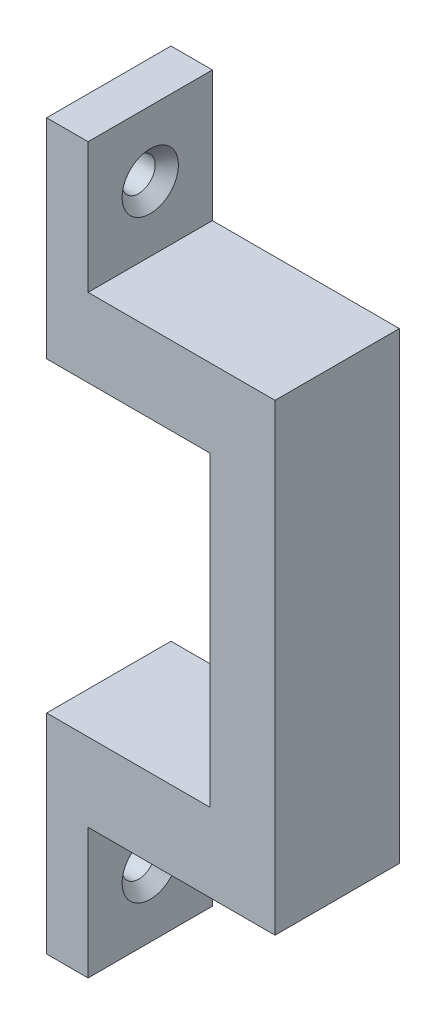
SolidWorks part; units mm, degrees
material "ABS"
ref_plane "Front" through (0, 0, 0) normal (0, 0, 1) x (1, 0, 0)
ref_plane "Top" through (0, 0, 0) normal (0, 1, 0) x (1, 0, 0)
ref_plane "Right" through (0, 0, 0) normal (1, 0, 0) x (0, 0, -1)
sketch "Sketch1" plane through (0, 0, 0) normal (0, 0, 1) x (1, 0, 0)
  line L0 (0, 11.75) -> (0, -11.75)
  line L1 (0, 11.75) -> (-12.5, 11.75)
  line L2 (-12.5, 11.75) -> (-12.5, 27.75)
  line L3 (-12.5, 27.75) -> (-9.325, 27.75)
  line L4 (-9.325, 27.75) -> (-9.325, 17.75)
  line L5 (-9.325, 17.75) -> (5, 17.75)
  line L6 (5, 17.75) -> (5, -17.75)
  line L7 (5, -17.75) -> (-9.325, -17.75)
  line L8 (-9.325, -17.75) -> (-9.325, -27.75)
  line L9 (-9.325, -27.75) -> (-12.5, -27.75)
  line L10 (-12.5, -27.75) -> (-12.5, -11.75)
  line L11 (-12.5, -11.75) -> (0, -11.75)
  point P4 (0, 0)
  dimension "D1" = 12.5
  dimension "D2" = 23.5
  dimension "D3" = 6
  dimension "D4" = 5
  dimension "D5" = 10
  dimension "D6" = 3.175
extrude "Boss-Extrude1" add sketch "Sketch1" along normal blind 9.525
sketch "Sketch2" plane through (0, 0, 0) normal (0, 0, -1) x (-1, 0, 0)
  line L0 (6.25, 11.75) -> (6.25, 17.75) construction
  line L1 (12.5, 11.75) -> (0, 11.75) construction
  line L2 (-5, 17.75) -> (9.325, 17.75) construction
  line L3 (6.25, -11.75) -> (6.25, -17.75) construction
  line L4 (0, -11.75) -> (12.5, -11.75) construction
  line L5 (9.325, -17.75) -> (-5, -17.75) construction
  point P12 (6.25, 14)
  point P13 (6.25, -14)
  dimension "D1" = 2.25
  dimension "D2" = 2.25
hole_wizard "#2 Clearance Hole1" positions "Sketch3" profile "Sketch4" hole size "#2" standard "ANSI Inch"
sketch "Sketch3" plane through (0, 0, 0) normal (0, 0, -1) x (-1, 0, 0)
  point P0 (6.25, 14)
  point P3 (6.25, -14)
sketch "Sketch4" plane through (-6.25, 14, 0) normal (1, 0, 0) x (0, 1, 0)
  line L0 (0, 0) -> (0, 6.9605)
  line L1 (0, 6.9605) -> (1.016, 6.35)
  line L2 (1.016, 6.35) -> (1.016, 0)
  line L5 (1.016, 0) -> (0, 0)
  line L10 (0, 6.9605) -> (-1.016, 6.35) construction
  line L11 (0, -6.35) -> (0, 107.95) construction
  dimension "Hole Dia." = 2.032
  dimension "Hole Depth" = 6.35
  dimension "Drill Angle" = 118
hole_wizard "#3 Clearance Hole2" positions "Sketch5" profile "Sketch6" hole size "#3" standard "ANSI Inch" end condition through all
sketch "Sketch5" plane through (-9.325, 0, 0) normal (1, 0, 0) x (0, 0, -1)
  line L0 (-4.7625, -17.75) -> (-4.7625, -27.75) construction
  line L1 (-9.525, -17.75) -> (0, -17.75) construction
  line L2 (-9.525, -27.75) -> (0, -27.75) construction
  line L4 (-4.7625, 17.75) -> (-4.7625, 27.75) construction
  line L5 (-9.525, 17.75) -> (0, 17.75) construction
  line L6 (-9.525, 27.75) -> (0, 27.75) construction
  point P0 (-4.7625, 22.75)
  point P2 (-4.7625, -22.75)
sketch "Sketch6" plane through (-9.325, 22.75, 4.7625) normal (0, 1, 0) x (0, 0, -1)
  line L0 (0, 0) -> (0, 3.175)
  line L1 (0, 3.175) -> (1.27, 3.175)
  line L2 (1.27, 3.175) -> (1.27, 0.889)
  line L3 (1.27, 0.889) -> (2.159, 0)
  line L5 (2.159, 0) -> (0, 0)
  line L6 (-1.27, 0.889) -> (-2.159, 0) construction
  line L11 (0, -6.35) -> (0, 107.95) construction
  dimension "Thru Hole Dia." = 2.54
  dimension "Thru Hole Depth" = 3.175
  dimension "Near C'Sink Dia." = 4.318
  dimension "Near C'Sink Angle" = 90
